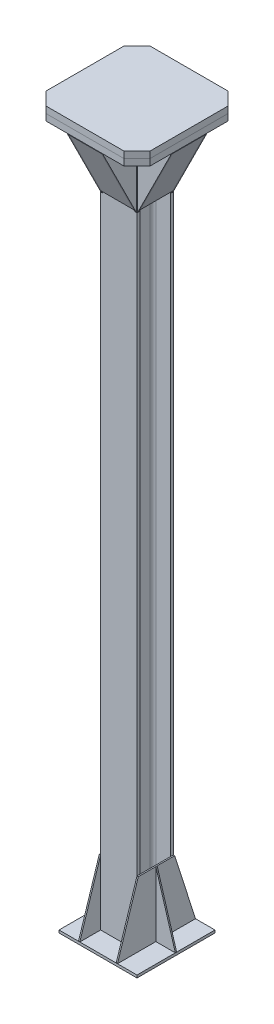
SolidWorks part; units mm, degrees
material "1.0037 (S235JR)"
ref_plane "Płaszczyzna przednia" through (0, 0, 0) normal (0, 0, 1) x (1, 0, 0)
ref_plane "Płaszczyzna górna" through (0, 0, 0) normal (0, 1, 0) x (1, 0, 0)
ref_plane "Płaszczyzna prawa" through (0, 0, 0) normal (1, 0, 0) x (0, 0, -1)
sketch "Szkic1" plane through (0, 0, 0) normal (0, 0, 1) x (1, 0, 0)
  line L0 (0, 0) -> (0, 2720)
  dimension "D1" = 2720
other "Człon konstrukcyjny1"
ref_plane "Płaszczyzna1" through (0, 0, 0) normal (0, 1, 0) x (-1, 0, 0)
sketch "Sketch11" plane through (0, 0, 0) normal (0, 1, 0) x (-1, 0, 0)
  line L0 (-70, -70) -> (-70, -58)
  line L1 (-70, -58) -> (-15.5, -58)
  line L2 (-3.5, -46) -> (-3.5, 46)
  line L3 (-15.5, 58) -> (-70, 58)
  line L4 (-70, 58) -> (-70, 70)
  line L5 (-70, 70) -> (70, 70)
  line L6 (70, 70) -> (70, 58)
  line L7 (70, 58) -> (15.5, 58)
  line L8 (3.5, 46) -> (3.5, -46)
  line L9 (15.5, -58) -> (70, -58)
  line L10 (70, -58) -> (70, -70)
  line L11 (70, -70) -> (-70, -70)
  line L12 (0, 0) -> (0, 70) construction
  line L13 (-3.5, 0) -> (3.5, 0) construction
  arc A0 (-15.5, -58) -> (-3.5, -46) centre (-15.5, -46) ccw
  arc A1 (-3.5, 46) -> (-15.5, 58) centre (-15.5, 46) ccw
  arc A2 (15.5, 58) -> (3.5, 46) centre (15.5, 46) ccw
  arc A3 (3.5, -46) -> (15.5, -58) centre (15.5, -46) ccw
  point P23 (0, 0)
  point P25 (0, -70)
  dimension "Ri" = 12
  dimension "Tw" = 7
  dimension "Bf" = 140
  dimension "Depth" = 140
  dimension "Tf" = 12
sketch "Szkic4" plane through (0, 0, 0) normal (0, -1, 0) x (1, 0, 0)
  line L1 (-150, 150) -> (150, 150)
  line L2 (-150, 150) -> (-150, -150)
  line L3 (-150, -150) -> (150, -150)
  line L4 (150, 150) -> (150, -150)
  line L5 (-150, 150) -> (150, -150) construction
  line L6 (-150, -150) -> (150, 150) construction
  point P0 (0, 0)
  dimension "D1" = 300
  dimension "D2" = 300
extrude "Dodanie-wyciągnięcie1" add sketch "Szkic4" along normal blind 10 separate body
sketch "Szkic6" plane through (0, 2720, 0) normal (0, 1, 0) x (1, 0, 0)
  line L1 (-200, 200) -> (200, 200)
  line L2 (-200, 200) -> (-200, -200)
  line L3 (-200, -200) -> (200, -200)
  line L4 (200, 200) -> (200, -200)
  line L5 (-200, 200) -> (200, -200) construction
  line L6 (-200, -200) -> (200, 200) construction
  point P0 (0, 0)
  dimension "D1" = 400
  dimension "D2" = 400
extrude "Dodanie-wyciągnięcie2" add sketch "Szkic6" along normal blind 25 separate body
chamfer "Sfazowanie1" distance 50 angle 45 4 edges at (-200, 2732.5, -200) (200, 2732.5, -200) (200, 2732.5, 200) (-200, 2732.5, 200)
ref_plane "Płaszczyzna2" through (0, 2745, 0) normal (0, 1, 0) x (1, 0, 0)
mirror "Lustro1" about plane through (0, 2745, 0) normal (0, 1, 0) of bodies 103
ref_plane "Płaszczyzna3" through (0, 0, 70) normal (0, 0, 1) x (1, 0, 0)
ref_plane "Płaszczyzna7" through (0, 0, 58) normal (0, 0, -1) x (-1, 0, 0)
ref_plane "Płaszczyzna8" through (-63, 0, 0) normal (-1, 0, 0) x (0, 0, 1)
sketch "Szkic10" plane through (-63, 0, 0) normal (-1, 0, 0) x (0, 0, 1)
  line L0 (195, 2720) -> (70, 2470)
  line L4 (200, 2745) -> (200, 2720) construction
  dimension "D1" = 5
  dimension "D2" = 250
extrude "Wyciągnięcie-cienka ścianka2" add sketch "Szkic10" against normal blind 126 separate body thin thin type one direction reverse wall 5
ref_plane "Płaszczyzna10" through (-63, 0, 0) normal (-1, 0, 0) x (0, 0, 1)
sketch "Szkic12" plane through (-63, 0, 0) normal (-1, 0, 0) x (0, 0, 1)
  line L0 (70, 2720) -> (70, 2458.8197)
  line L2 (199.4721, 2717.7639) -> (74.4721, 2467.7639) construction
  line L3 (200.5902, 2720) -> (70, 2458.8197)
  line L4 (70, 2720) -> (200.5902, 2720)
extrude "Dodanie-wyciągnięcie4" add sketch "Szkic12" along normal blind 5 separate body
ref_plane "Płaszczyzna11" through (0, 0, 0) normal (-1, 0, 0) x (0, 0, 1)
mirror "Lustro2" about plane through (0, 0, 0) normal (-1, 0, 0) of bodies 108
ref_plane "Płaszczyzna12" through (0, 0, 0) normal (0, 0, 1) x (1, 0, 0)
ref_plane "Płaszczyzna13" through (0, 0, 68) normal (0, 0, 1) x (1, 0, 0)
pattern_circular "Szyk kołowy1" count 4 over 360 about axis through (0, 0, 0) along (0, 1, 0) of bodies 108 109 107
ref_plane "Płaszczyzna15" through (70, 0, 0) normal (1, 0, 0) x (0, 0, -1)
sketch "Szkic18" plane through (70, 0, 0) normal (1, 0, 0) x (0, 0, -1)
  line L0 (-150, 0) -> (-70, 250)
  line L1 (-70, 2720) -> (-70, 0) construction
  line L2 (-70, 250) -> (70, 250)
  line L3 (70, 2720) -> (70, 0) construction
  line L4 (70, 250) -> (150, 0)
  line L5 (150, 0) -> (-150, 0)
  dimension "D1" = 250
extrude "Dodanie-wyciągnięcie5" add sketch "Szkic18" along normal blind 5 separate body
ref_plane "Płaszczyzna16" through (0, 0, 0) normal (0, 0, 1) x (1, 0, 0)
sketch "Szkic20" plane through (0, 0, 0) normal (0, 0, 1) x (1, 0, 0)
  line L0 (75, 250) -> (150, 0)
  line L1 (75, 250) -> (75, 0)
  line L2 (150, 0) -> (-150, 0) construction
  line L3 (75, 250) -> (75, 0) construction
  line L4 (75, 0) -> (150, 0)
extrude "Dodanie-wyciągnięcie6" add sketch "Szkic20" along normal mid plane 5 separate body
ref_plane "Płaszczyzna17" through (0, 0, 0) normal (1, 0, 0) x (0, 0, -1)
mirror "Lustro4" about plane through (0, 0, 0) normal (1, 0, 0) of bodies 123 124
